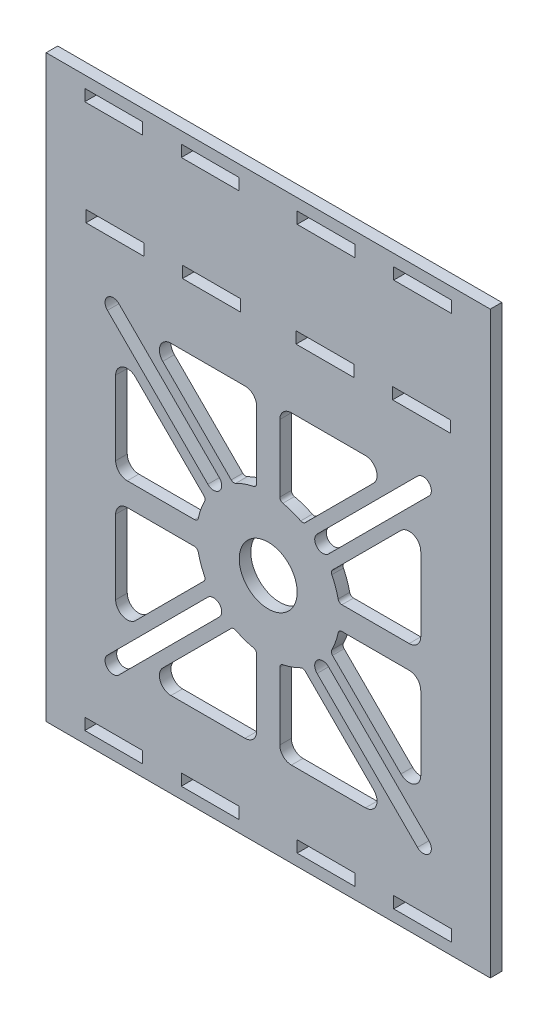
SolidWorks part; units mm, degrees
ref_plane "Front Plane" through (0, 0, 0) normal (0, 0, 1) x (1, 0, 0)
ref_plane "Top Plane" through (0, 0, 0) normal (0, 1, 0) x (1, 0, 0)
ref_plane "Right Plane" through (0, 0, 0) normal (1, 0, 0) x (0, 0, -1)
sketch "Sketch1" plane through (0, 0, 0) normal (0, 0, 1) x (1, 0, 0)
  line L0 (0, 82.3583) -> (0, -86.853) construction
  line L1 (-57.5, 75) -> (57.5, 75)
  line L2 (-57.5, 75) -> (-57.5, -75)
  line L3 (-57.5, -75) -> (57.5, -75)
  line L4 (57.5, 75) -> (57.5, -75)
  line L5 (-57.5, 75) -> (57.5, -75) construction
  line L6 (-57.5, -75) -> (57.5, 75) construction
  line L7 (-69.8445, 0) -> (74.4392, 0) construction
  line L8 (-74.4542, 72) -> (67.0637, 72) construction
  line L9 (-74.4542, -72) -> (67.0637, -72) construction
  line L10 (7.5, 72) -> (7.5, 69)
  line L11 (-47.5, 72) -> (-32.5, 72)
  line L12 (-47.5, 72) -> (-47.5, 69)
  line L13 (-47.5, 69) -> (-32.5, 69)
  line L14 (-32.5, 72) -> (-32.5, 69)
  line L15 (-22.5, 72) -> (-7.5, 72)
  line L16 (-22.5, 72) -> (-22.5, 69)
  line L17 (-22.5, 69) -> (-7.5, 69)
  line L18 (-7.5, 72) -> (-7.5, 69)
  line L19 (22.5, 69) -> (7.5, 69)
  line L20 (22.5, 72) -> (7.5, 72)
  line L21 (22.5, 72) -> (22.5, 69)
  line L22 (32.5, 72) -> (32.5, 69)
  line L23 (47.5, 69) -> (32.5, 69)
  line L24 (47.5, 72) -> (32.5, 72)
  line L25 (47.5, 72) -> (47.5, 69)
  line L26 (47.5, -72) -> (47.5, -69)
  line L27 (47.5, -72) -> (32.5, -72)
  line L28 (47.5, -69) -> (32.5, -69)
  line L29 (32.5, -72) -> (32.5, -69)
  line L30 (22.5, -72) -> (22.5, -69)
  line L31 (22.5, -72) -> (7.5, -72)
  line L32 (22.5, -69) -> (7.5, -69)
  line L33 (-7.5, -72) -> (-7.5, -69)
  line L34 (-22.5, -69) -> (-7.5, -69)
  line L35 (-22.5, -72) -> (-22.5, -69)
  line L36 (-22.5, -72) -> (-7.5, -72)
  line L37 (-32.5, -72) -> (-32.5, -69)
  line L38 (-47.5, -69) -> (-32.5, -69)
  line L39 (-47.5, -72) -> (-47.5, -69)
  line L40 (-47.5, -72) -> (-32.5, -72)
  line L41 (7.5, -72) -> (7.5, -69)
  line L42 (-66.5551, 43.5) -> (62.3228, 43.5) construction
  line L43 (7.2, 45) -> (7.2, 42)
  line L44 (-47.2, 45) -> (-32.2, 45)
  line L45 (-47.2, 45) -> (-47.2, 42)
  line L46 (-47.2, 42) -> (-32.2, 42)
  line L47 (-32.2, 45) -> (-32.2, 42)
  line L48 (-7.2, 45) -> (-22.2, 45)
  line L49 (-7.2, 45) -> (-7.2, 42)
  line L50 (-7.2, 42) -> (-22.2, 42)
  line L51 (-22.2, 45) -> (-22.2, 42)
  line L52 (7.2, 45) -> (22.2, 45)
  line L53 (7.2, 42) -> (22.2, 42)
  line L54 (22.2, 45) -> (22.2, 42)
  line L55 (32.2, 45) -> (32.2, 42)
  line L56 (47.2, 42) -> (32.2, 42)
  line L57 (47.2, 45) -> (47.2, 42)
  line L58 (47.2, 45) -> (32.2, 45)
  line L59 (0, -63.2785) -> (0, 36.7215) construction
  line L60 (-75.2921, -13.5) -> (68.6825, -13.5) construction
  line L61 (0, -66.6716) -> (0, 39.6716) construction
  line L62 (39.5, -7.5) -> (39.5, 11.6863)
  line L63 (0, -13.5) -> (41.6493, -13.5) construction
  line L64 (19.0853, -10.5) -> (36.5, -10.5)
  line L65 (16.6552, -3.9159) -> (34.3787, 13.8076)
  line L66 (3, -32.5853) -> (3, -50)
  line L67 (0, -13.5) -> (43.1262, 29.6262) construction
  line L68 (6, -53) -> (25.1863, -53)
  line L69 (9.5841, -30.1552) -> (27.3076, -47.8787)
  line L70 (16.6552, -23.0841) -> (34.3787, -40.8076)
  line L71 (6, 26) -> (25.1863, 26)
  line L72 (19.0853, -16.5) -> (36.5, -16.5)
  line L73 (39.5, -19.5) -> (39.5, -38.6863)
  line L74 (-3, 5.5853) -> (-3, 23)
  line L75 (3, 5.5853) -> (3, 23)
  line L76 (9.5841, 3.1552) -> (27.3076, 20.8787)
  line L77 (-6, 26) -> (-25.1863, 26)
  line L78 (-9.5841, 3.1552) -> (-27.3076, 20.8787)
  line L79 (-39.5, -7.5) -> (-39.5, 11.6863)
  line L80 (-19.0853, -10.5) -> (-36.5, -10.5)
  line L81 (-16.6552, -3.9159) -> (-34.3787, 13.8076)
  line L82 (-19.0853, -16.5) -> (-36.5, -16.5)
  line L83 (-16.6552, -23.0841) -> (-34.3787, -40.8076)
  line L84 (-39.5, -19.5) -> (-39.5, -38.6863)
  line L85 (-3, -32.5853) -> (-3, -50)
  line L86 (-9.5841, -30.1552) -> (-27.3076, -47.8787)
  line L87 (-6, -53) -> (-25.1863, -53)
  line L88 (0, -13.5) -> (0, -17.5318) construction
  line L89 (0, -13.5) -> (45.8967, -13.5) construction
  line L90 (0, -13.5) -> (50.75, 37.25) construction
  line L91 (14.1421, 0.6421) -> (40.1434, 26.6434) construction
  line L92 (12.6572, 2.1271) -> (38.6585, 28.1283)
  line L93 (15.6271, -0.8428) -> (41.6283, 25.1585)
  line L94 (14.1421, -27.6421) -> (40.1434, -53.6434) construction
  line L95 (12.6572, -29.1271) -> (38.6585, -55.1283)
  line L96 (15.6271, -26.1572) -> (41.6283, -52.1585)
  line L97 (-14.1421, -27.6421) -> (-40.1434, -53.6434) construction
  line L98 (-12.6572, -29.1271) -> (-38.6585, -55.1283)
  line L99 (-15.6271, -26.1572) -> (-41.6283, -52.1585)
  line L100 (-14.1421, 0.6421) -> (-40.1434, 26.6434) construction
  line L101 (-12.6572, 2.1271) -> (-38.6585, 28.1283)
  line L102 (-15.6271, -0.8428) -> (-41.6283, 25.1585)
  circle A0 centre (0, -13.5) radius 7.5
  arc A1 (3.7949, -31.6066) -> (3, -32.5853) centre (4, -32.5853) ccw
  arc A2 (8.4218, 2.9719) -> (3.7949, 4.6066) centre (0, -13.5) ccw
  arc A3 (8.4218, -29.9719) -> (3.7949, -31.6066) centre (0, -13.5) cw
  arc A4 (27.3076, 20.8787) -> (25.1863, 26) centre (25.1863, 23) ccw
  arc A5 (3, 23) -> (6, 26) centre (6, 23) cw
  arc A6 (9.5841, 3.1552) -> (8.4218, 2.9719) centre (8.877, 3.8623) cw
  arc A7 (3.7949, 4.6066) -> (3, 5.5853) centre (4, 5.5853) cw
  arc A8 (36.5, -10.5) -> (39.5, -7.5) centre (36.5, -7.5) ccw
  arc A9 (18.1066, -9.7051) -> (19.0853, -10.5) centre (19.0853, -9.5) ccw
  arc A10 (16.4719, -5.0782) -> (18.1066, -9.7051) centre (0, -13.5) cw
  arc A11 (16.6552, -3.9159) -> (16.4719, -5.0782) centre (17.3623, -4.623) ccw
  arc A12 (34.3787, 13.8076) -> (39.5, 11.6863) centre (36.5, 11.6863) cw
  arc A13 (9.5841, -30.1552) -> (8.4218, -29.9719) centre (8.877, -30.8623) ccw
  arc A14 (3, -50) -> (6, -53) centre (6, -50) ccw
  arc A15 (27.3076, -47.8787) -> (25.1863, -53) centre (25.1863, -50) cw
  arc A16 (16.6552, -23.0841) -> (16.4719, -21.9218) centre (17.3623, -22.377) cw
  arc A17 (16.4719, -21.9218) -> (18.1066, -17.2949) centre (0, -13.5) ccw
  arc A18 (18.1066, -17.2949) -> (19.0853, -16.5) centre (19.0853, -17.5) cw
  arc A19 (36.5, -16.5) -> (39.5, -19.5) centre (36.5, -19.5) cw
  arc A20 (34.3787, -40.8076) -> (39.5, -38.6863) centre (36.5, -38.6863) ccw
  arc A21 (-3.7949, 4.6066) -> (-3, 5.5853) centre (-4, 5.5853) ccw
  arc A22 (-8.4218, 2.9719) -> (-3.7949, 4.6066) centre (0, -13.5) cw
  arc A23 (-9.5841, 3.1552) -> (-8.4218, 2.9719) centre (-8.877, 3.8623) ccw
  arc A24 (-3, 23) -> (-6, 26) centre (-6, 23) ccw
  arc A25 (-27.3076, 20.8787) -> (-25.1863, 26) centre (-25.1863, 23) cw
  arc A26 (-34.3787, 13.8076) -> (-39.5, 11.6863) centre (-36.5, 11.6863) ccw
  arc A27 (-36.5, -10.5) -> (-39.5, -7.5) centre (-36.5, -7.5) cw
  arc A28 (-18.1066, -9.7051) -> (-19.0853, -10.5) centre (-19.0853, -9.5) cw
  arc A29 (-16.6552, -3.9159) -> (-16.4719, -5.0782) centre (-17.3623, -4.623) cw
  arc A30 (-16.4719, -5.0782) -> (-18.1066, -9.7051) centre (0, -13.5) ccw
  arc A31 (-16.6552, -23.0841) -> (-16.4719, -21.9218) centre (-17.3623, -22.377) ccw
  arc A32 (-16.4719, -21.9218) -> (-18.1066, -17.2949) centre (0, -13.5) cw
  arc A33 (-18.1066, -17.2949) -> (-19.0853, -16.5) centre (-19.0853, -17.5) ccw
  arc A34 (-36.5, -16.5) -> (-39.5, -19.5) centre (-36.5, -19.5) ccw
  arc A35 (-34.3787, -40.8076) -> (-39.5, -38.6863) centre (-36.5, -38.6863) cw
  arc A36 (-9.5841, -30.1552) -> (-8.4218, -29.9719) centre (-8.877, -30.8623) cw
  arc A37 (-8.4218, -29.9719) -> (-3.7949, -31.6066) centre (0, -13.5) ccw
  arc A38 (-3.7949, -31.6066) -> (-3, -32.5853) centre (-4, -32.5853) cw
  arc A39 (-3, -50) -> (-6, -53) centre (-6, -50) cw
  arc A40 (-27.3076, -47.8787) -> (-25.1863, -53) centre (-25.1863, -50) ccw
  arc A41 (12.6572, 2.1271) -> (15.6271, -0.8428) centre (14.1421, 0.6421) ccw
  arc A42 (41.6283, 25.1585) -> (38.6585, 28.1283) centre (40.1434, 26.6434) ccw
  arc A43 (12.6572, -29.1271) -> (15.6271, -26.1572) centre (14.1421, -27.6421) cw
  arc A44 (41.6283, -52.1585) -> (38.6585, -55.1283) centre (40.1434, -53.6434) cw
  arc A45 (-12.6572, -29.1271) -> (-15.6271, -26.1572) centre (-14.1421, -27.6421) ccw
  arc A46 (-41.6283, -52.1585) -> (-38.6585, -55.1283) centre (-40.1434, -53.6434) ccw
  arc A47 (-12.6572, 2.1271) -> (-15.6271, -0.8428) centre (-14.1421, 0.6421) cw
  arc A48 (-41.6283, 25.1585) -> (-38.6585, 28.1283) centre (-40.1434, 26.6434) cw
  point P0 (0, 0)
  point P64 (0, -13.5)
  point P65 (0, 0)
  point P70 (0, 0)
  point P176 (0, -13.5)
  point P180 (27.1428, 13.6428)
  point P187 (27.1428, -40.6428)
  point P194 (-27.1428, -40.6428)
  point P201 (-27.1428, 13.6428)
  point P206 (0, 0)
  point P207 (0, 0)
  dimension "D1" = 115
  dimension "D2" = 150
  dimension "D3" = 3
  dimension "D4" = 10
  dimension "D5" = 15
  dimension "D6" = 3
  dimension "D7" = 10
  dimension "D8" = 15
  dimension "D9" = 3
  dimension "D10" = 7.5
  dimension "D11" = 118.5
  dimension "D12" = 1.5
  dimension "D13" = 3
  dimension "D14" = 15
  dimension "D15" = 15
  dimension "D16" = 10
  dimension "D17" = 3
  dimension "D18" = 1.5
  dimension "D19" = 55.5
extrude "Boss-Extrude1" add sketch "Sketch1" along normal blind 3
